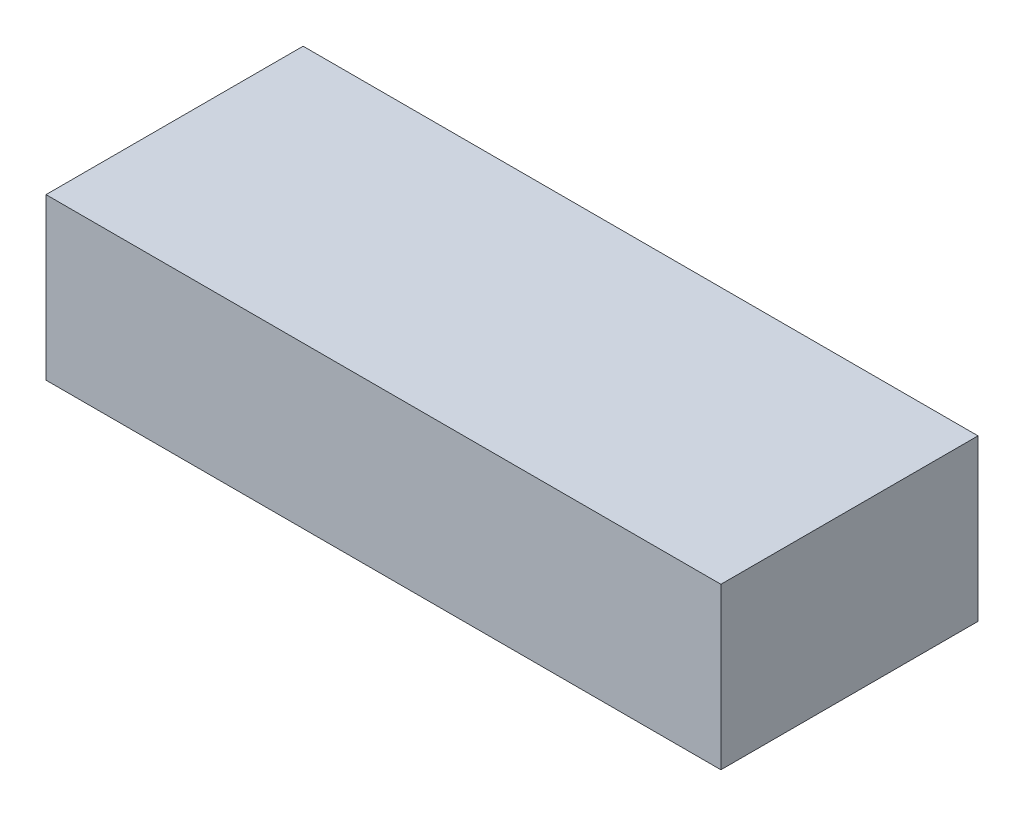
SolidWorks part; units mm, degrees
ref_plane "Front Plane" through (0, 0, 0) normal (0, 0, 1) x (1, 0, 0)
ref_plane "Top Plane" through (0, 0, 0) normal (0, 1, 0) x (1, 0, 0)
ref_plane "Right Plane" through (0, 0, 0) normal (1, 0, 0) x (0, 0, -1)
sketch "Sketch1" plane through (0, 0, 0) normal (0, 1, 0) x (1, 0, 0)
  line L1 (0, 0) -> (66.675, 0)
  line L2 (0, 0) -> (0, 25.4)
  line L3 (0, 25.4) -> (66.675, 25.4)
  line L4 (66.675, 0) -> (66.675, 25.4)
  dimension "D1" = 66.675
  dimension "D2" = 25.4
extrude "Boss-Extrude1" add sketch "Sketch1" along normal blind 15.875
